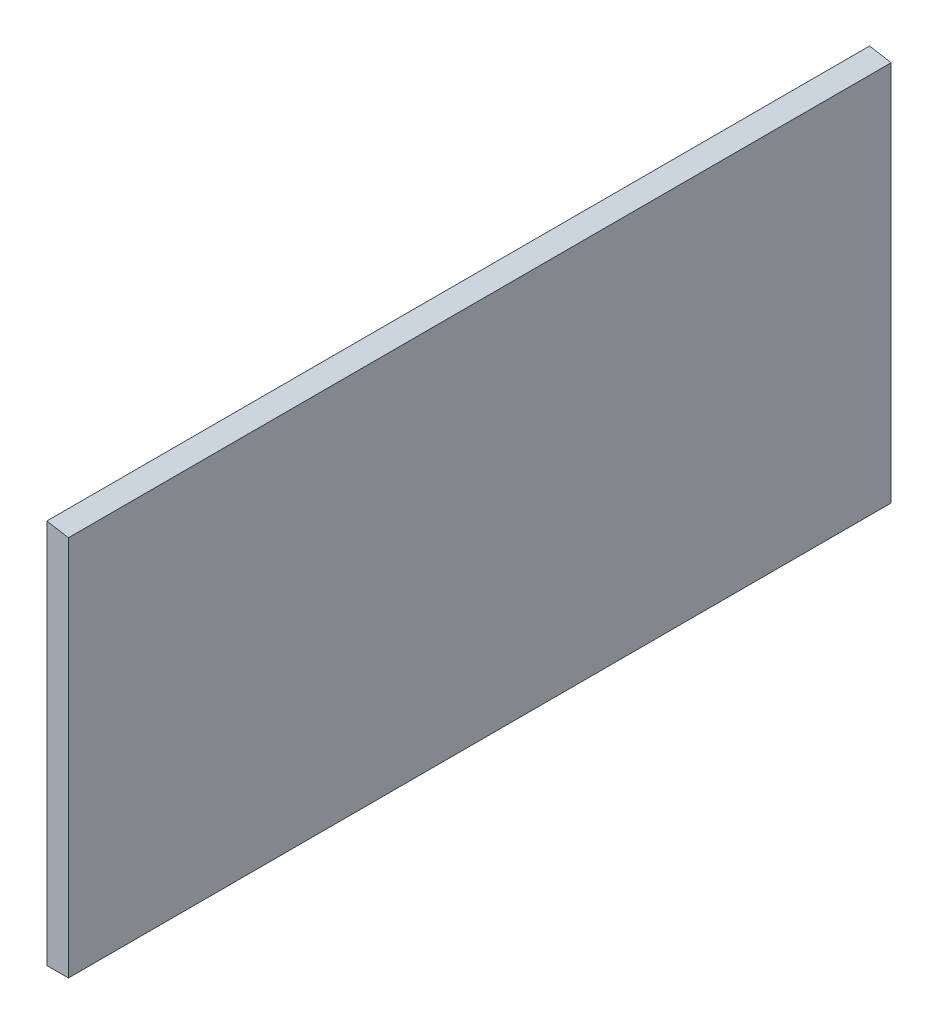
SolidWorks part; units mm, degrees
ref_plane "Front Plane" through (0, 0, 0) normal (0, 0, 1) x (1, 0, 0)
ref_plane "Top Plane" through (0, 0, 0) normal (0, 1, 0) x (1, 0, 0)
ref_plane "Right Plane" through (0, 0, 0) normal (1, 0, 0) x (0, 0, -1)
sketch "Sketch1" plane through (0, 0, 0) normal (0, 0, 1) x (1, 0, 0)
  line L0 (3, 0) -> (3, 52.9186)
  line L1 (0, 53.428) -> (0, 0)
  line L2 (0, 0) -> (3, 0)
  line L3 (3, 52.9186) -> (0, 53.428)
  dimension "D1" = 3
  dimension "D2" = 53.428
  dimension "D3" = 52.9186
extrude "Boss-Extrude1" add sketch "Sketch1" along normal mid plane 114.188
